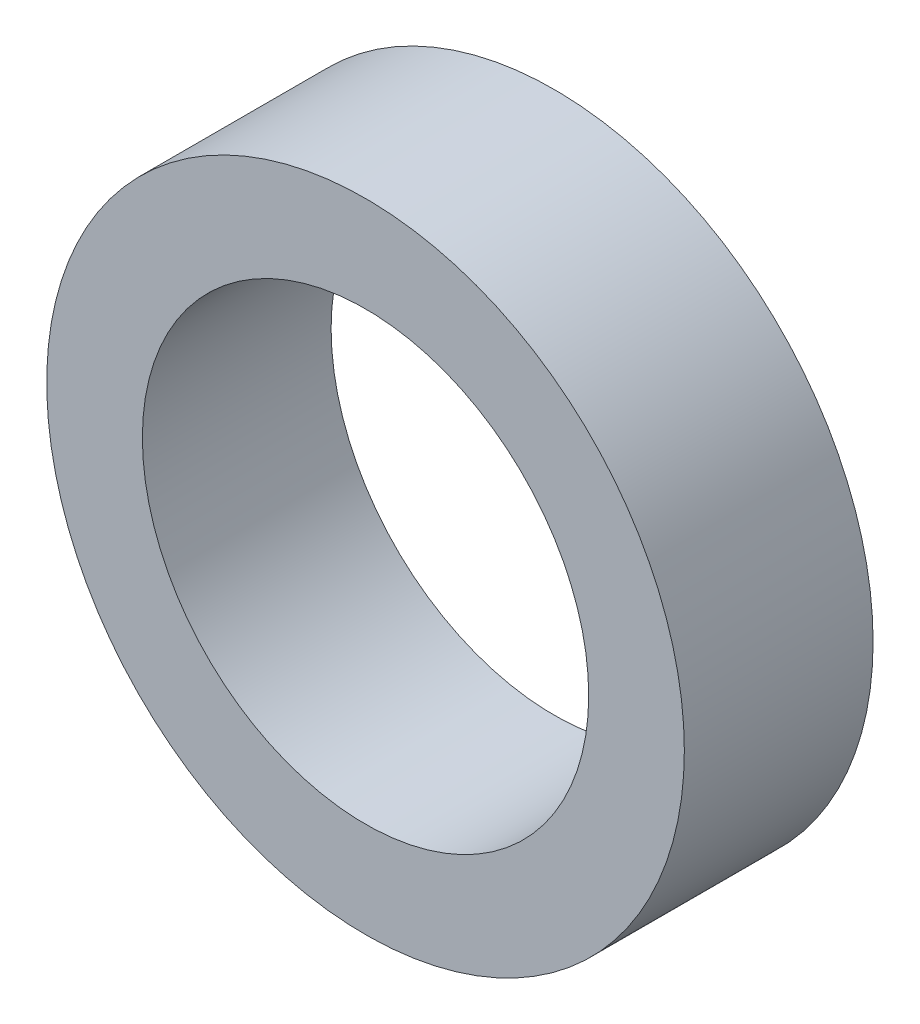
SolidWorks part; units mm, degrees
ref_plane "Front Plane" through (0, 0, 0) normal (0, 0, 1) x (1, 0, 0)
ref_plane "Top Plane" through (0, 0, 0) normal (0, 1, 0) x (1, 0, 0)
ref_plane "Right Plane" through (0, 0, 0) normal (1, 0, 0) x (0, 0, -1)
sketch "Sketch1" plane through (0, 0, 0) normal (0, 0, 1) x (1, 0, 0)
  circle A0 centre (0, 0) radius 15.875
  circle A1 centre (0, 0) radius 11.1125
  dimension "D1" = 22.225
  dimension "D2" = 31.75
extrude "Boss-Extrude1" add sketch "Sketch1" along normal mid plane 9.398
